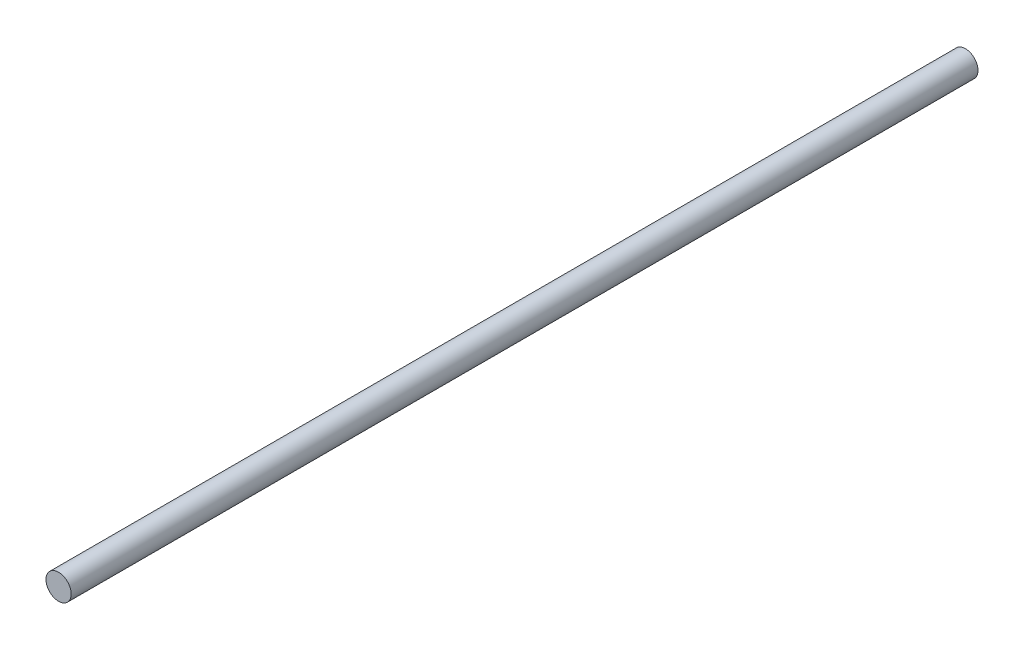
SolidWorks part; units mm, degrees
ref_plane "Front Plane" through (0, 0, 0) normal (0, 0, 1) x (1, 0, 0)
ref_plane "Top Plane" through (0, 0, 0) normal (0, 1, 0) x (1, 0, 0)
ref_plane "Right Plane" through (0, 0, 0) normal (1, 0, 0) x (0, 0, -1)
sketch "Sketch1" plane through (0, 0, 0) normal (0, 0, 1) x (1, 0, 0)
  circle A0 centre (0, 0) radius 6.35
extrude "Boss-Extrude1" add sketch "Sketch1" along normal blind 457.2
